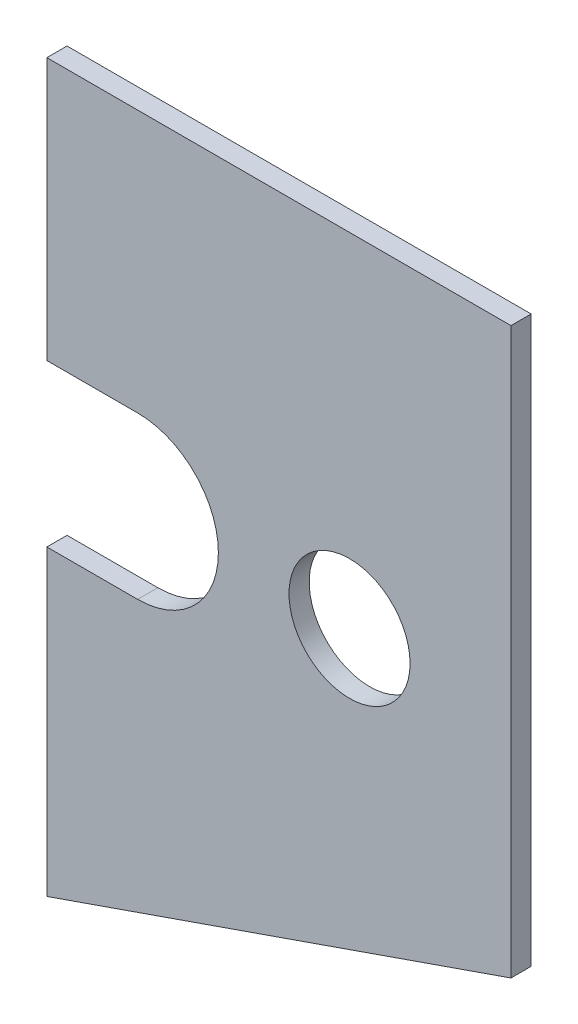
SolidWorks part; units mm, degrees
ref_plane "Front Plane" through (0, 0, 0) normal (0, 0, 1) x (1, 0, 0)
ref_plane "Top Plane" through (0, 0, 0) normal (0, 1, 0) x (1, 0, 0)
ref_plane "Right Plane" through (0, 0, 0) normal (1, 0, 0) x (0, 0, -1)
sketch "Sketch1" plane through (0, 0, 0) normal (0, 0, 1) x (1, 0, 0)
  line L0 (0, 0) -> (0, 228.6)
  line L1 (0, 228.6) -> (146.05, 228.6)
  line L2 (146.05, 228.6) -> (146.05, 50.8)
  line L3 (146.05, 50.8) -> (0, 0)
  dimension "D1" = 228.6
  dimension "D2" = 146.05
  dimension "D3" = 50.8
extrude "Boss-Extrude1" add sketch "Sketch1" along normal blind 6.35
sketch "Sketch2" plane through (0, 0, 6.35) normal (0, 0, 1) x (1, 0, 0)
  line L0 (0, 228.6) -> (0, 0) construction
  line L2 (0, 120.65) -> (28.575, 120.65) construction
  line L3 (0, 146.05) -> (28.575, 146.05)
  line L4 (0, 95.25) -> (28.575, 95.25)
  arc A0 (93.1519, 139.5841) -> (89.6911, 102.4291) centre (95.25, 120.65) cw construction
  circle A1 centre (95.25, 120.65) radius 19.05
  arc A2 (0, 146.05) -> (0, 95.25) centre (0, 120.65) ccw
  arc A3 (28.575, 95.25) -> (28.575, 146.05) centre (28.575, 120.65) ccw
  point P8 (14.2875, 120.65)
  dimension "D3" = 19.05
  dimension "D1" = 95.25
  dimension "D2" = 120.65
  dimension "D4" = 50.8
  dimension "D5" = 28.575
extrude "Cut-Extrude1" cut sketch "Sketch2" against normal through all
